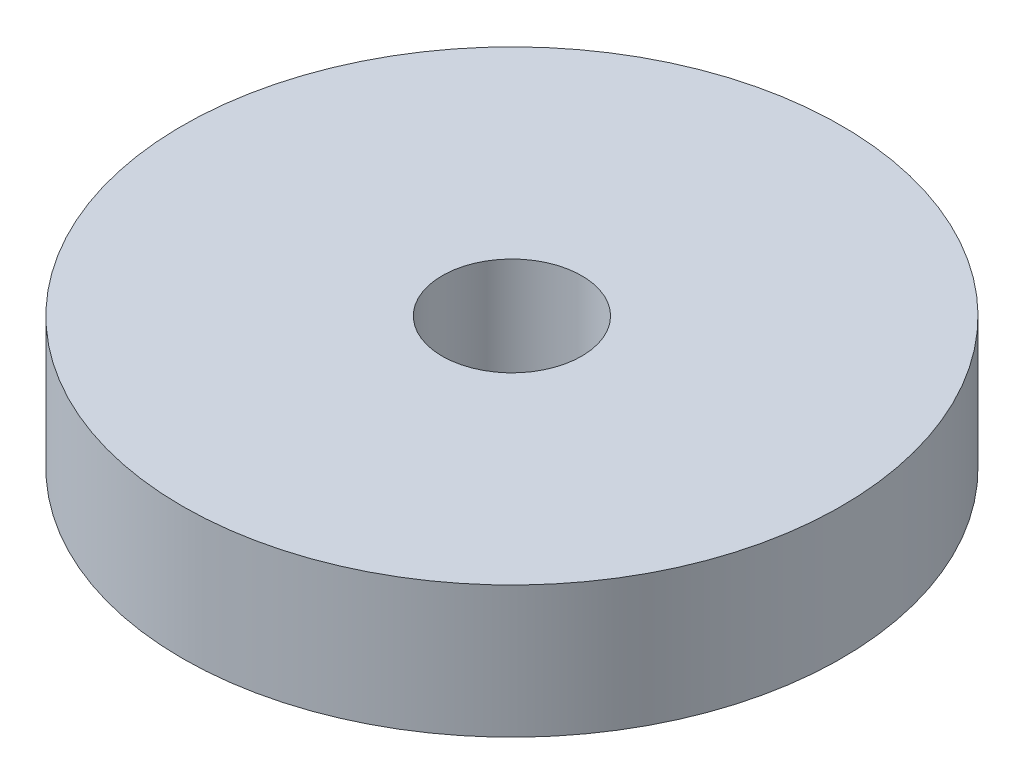
SolidWorks part; units mm, degrees
ref_plane "Front Plane" through (0, 0, 0) normal (0, 0, 1) x (1, 0, 0)
ref_plane "Top Plane" through (0, 0, 0) normal (0, 1, 0) x (1, 0, 0)
ref_plane "Right Plane" through (0, 0, 0) normal (1, 0, 0) x (0, 0, -1)
sketch "Sketch1" plane through (0, 0, 0) normal (0, 1, 0) x (1, 0, 0)
  circle A0 centre (0, 0) radius 29.9999
extrude "Boss-Extrude1" add sketch "Sketch1" along normal blind 12
sketch "Sketch2" plane through (0, 12, 0) normal (0, 1, 0) x (1, 0, 0)
  circle A0 centre (0, 0) radius 6.35
extrude "Cut-Extrude1" cut sketch "Sketch2" against normal blind 12
